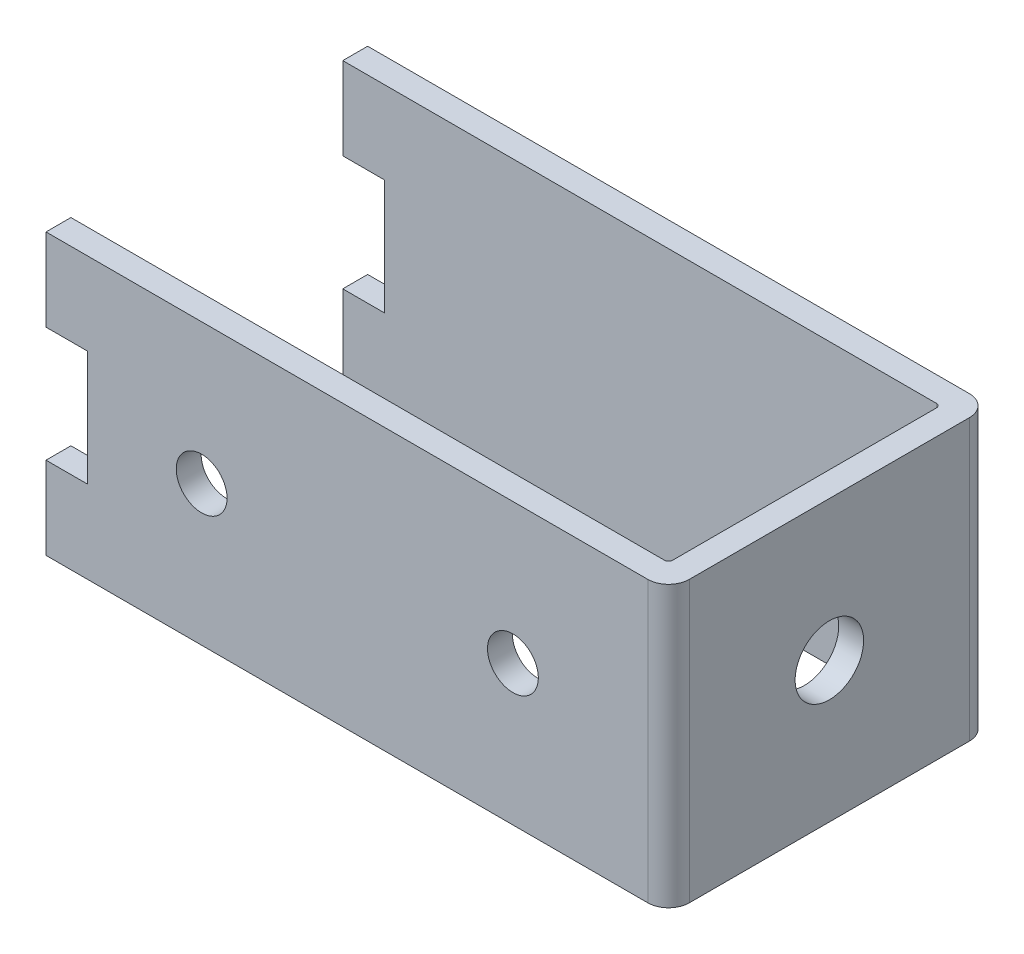
SolidWorks part; units mm, degrees
ref_plane "Alzado" through (0, 0, 0) normal (0, 0, 1) x (1, 0, 0)
ref_plane "Planta" through (0, 0, 0) normal (0, 1, 0) x (1, 0, 0)
ref_plane "Vista lateral" through (0, 0, 0) normal (1, 0, 0) x (0, 0, -1)
sketch "Croquis1" plane through (0, 0, 0) normal (0, 1, 0) x (1, 0, 0)
  line L0 (-15, 7.75) -> (15, -7.75) construction
  line L1 (-15, 7.75) -> (15, 7.75)
  line L2 (-15, 7.75) -> (-15, -7.75)
  line L3 (-15, -7.75) -> (15, -7.75)
  line L4 (15, 7.75) -> (15, -7.75)
  point P4 (0, 0)
  dimension "D1" = 15.5
  dimension "D2" = 30
extrude "Saliente-Extruir1" add sketch "Croquis1" along normal mid plane 13.5
sketch "Croquis2" plane through (0, 0, 0) normal (0, 1, 0) x (1, 0, 0)
  line L0 (-15, 7.75) -> (-15, -7.75) construction
  line L1 (-15, -6.55) -> (13.8, -6.55)
  line L2 (-15, -6.55) -> (-15, 6.55)
  line L3 (-15, 6.55) -> (13.8, 6.55)
  line L4 (13.8, -6.55) -> (13.8, 6.55)
  line L5 (15, 7.75) -> (-15, 7.75) construction
  line L6 (15, -7.75) -> (15, 7.75) construction
  point P6 (-15, 0)
  point P7 (-15, 0)
  dimension "D1" = 1.2
  dimension "D2" = 1.2
extrude "Cortar-Extruir1" cut sketch "Croquis2" against normal through all both and the other way through all
sketch "Croquis3" plane through (15, 0, 0) normal (1, 0, 0) x (0, 0, -1)
  circle A0 centre (0, 0) radius 1.65
  dimension "D1" = 3.3
extrude "Cortar-Extruir2" cut sketch "Croquis3" against normal up to next
fillet "Redondeo1" radius 1 2 edges at (15, 0, 7.75) (15, 0, -7.75)
fillet "Redondeo2" radius 0.2 2 edges at (13.8, 0, 6.55) (13.8, 0, -6.55)
sketch "Croquis4" plane through (0, 0, 0) normal (0, 0, 1) x (1, 0, 0)
  line L0 (-15, 6.75) -> (-15, -6.75) construction
  line L1 (-15, 2.775) -> (-13, 2.775)
  line L2 (-15, 2.775) -> (-15, -2.775)
  line L3 (-15, -2.775) -> (-13, -2.775)
  line L4 (-13, 2.775) -> (-13, -2.775)
  point P4 (-15, 0)
  point P7 (-15, 0)
  dimension "D1" = 5.55
  dimension "D2" = 2
extrude "Cortar-Extruir3" cut sketch "Croquis4" against normal through all both and the other way through all
sketch "Croquis5" plane through (0, 0, 7.75) normal (0, 0, 1) x (1, 0, 0)
  line L0 (15, 6.75) -> (15, -6.75) construction
  circle A0 centre (-7.5, 0) radius 1.225
  circle A1 centre (7.5, 0) radius 1.225
  dimension "D1" = 2.45
  dimension "D2" = 15
  dimension "D3" = 7.5
extrude "Cortar-Extruir4" cut sketch "Croquis5" against normal up to next
